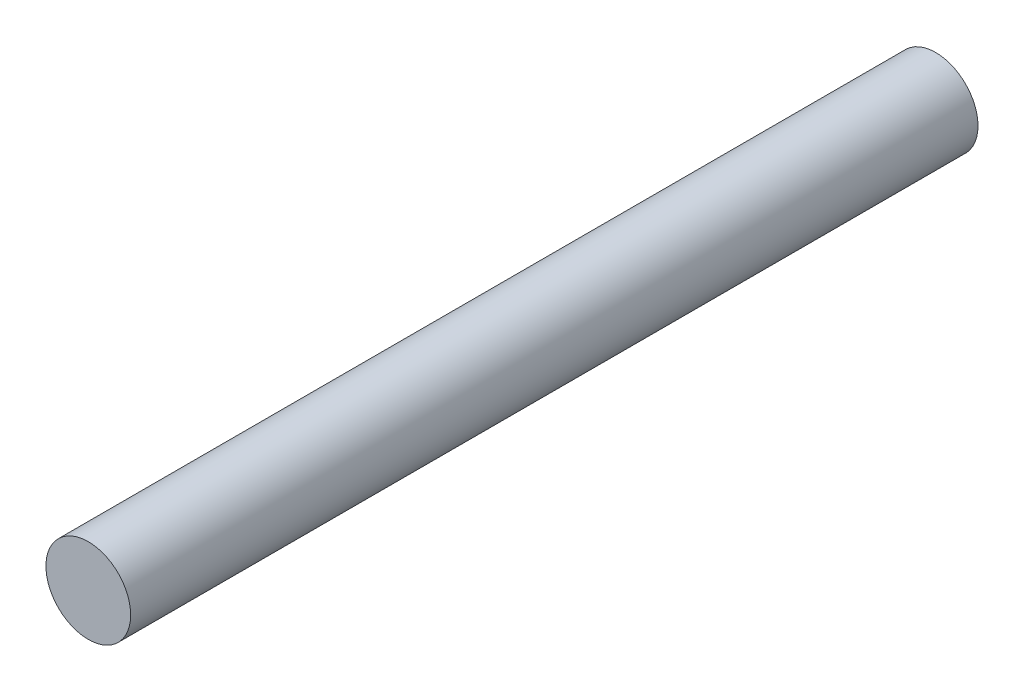
SolidWorks part; units mm, degrees
ref_plane "Front Plane" through (0, 0, 0) normal (0, 0, 1) x (1, 0, 0)
ref_plane "Top Plane" through (0, 0, 0) normal (0, 1, 0) x (1, 0, 0)
ref_plane "Right Plane" through (0, 0, 0) normal (1, 0, 0) x (0, 0, -1)
sketch "Sketch1" plane through (0, 0, 0) normal (0, 0, 1) x (1, 0, 0)
  circle A0 centre (0, 0) radius 10
  dimension "D1" = 20
extrude "Boss-Extrude1" add sketch "Sketch1" along normal blind 200
